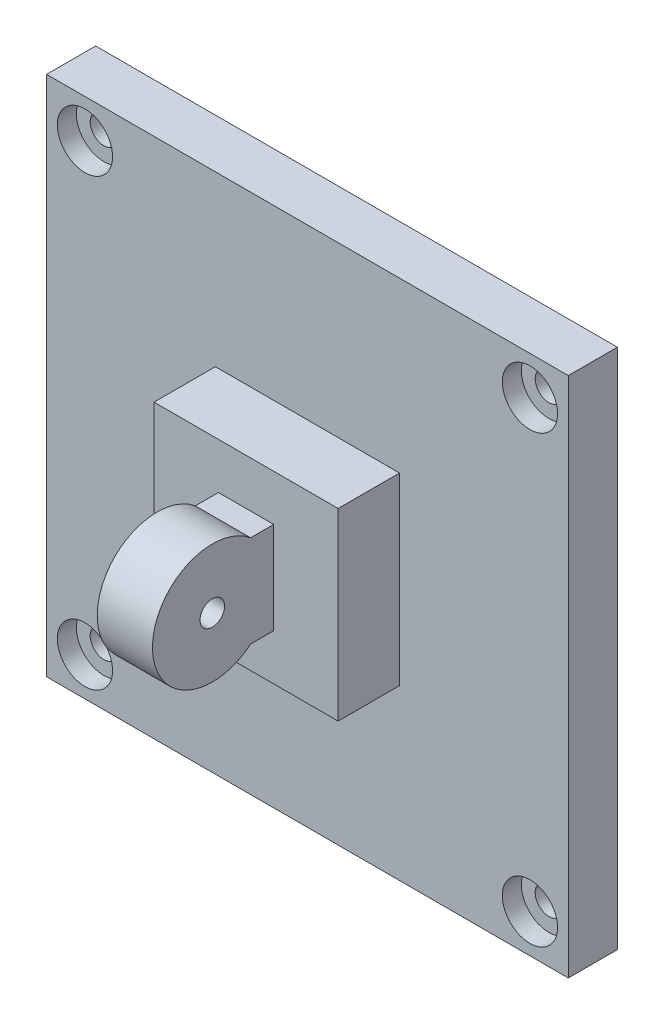
SolidWorks part; units mm, degrees
ref_plane "Front Plane" through (0, 0, 0) normal (0, 0, 1) x (1, 0, 0)
ref_plane "Top Plane" through (0, 0, 0) normal (0, 1, 0) x (1, 0, 0)
ref_plane "Right Plane" through (0, 0, 0) normal (1, 0, 0) x (0, 0, -1)
sketch "Esboço1" plane through (0, 0, 0) normal (0, 0, 1) x (1, 0, 0)
  line L0 (0, 36.75) -> (0, -36.75) construction
  line L9 (36.75, 0) -> (-36.75, 0) construction
  line L10 (-36.75, 36.75) -> (36.75, 36.75) construction
  line L11 (36.75, -36.75) -> (-36.75, -36.75) construction
  line L12 (-36.75, 36.75) -> (-36.75, -36.75) construction
  line L13 (36.75, 36.75) -> (36.75, -36.75) construction
  line L15 (-42.5, 42.5) -> (42.5, 42.5)
  line L16 (-42.5, 42.5) -> (-42.5, -42.5)
  line L17 (-42.5, -42.5) -> (42.5, -42.5)
  line L18 (42.5, 42.5) -> (42.5, -42.5)
  point P12 (0, 0)
  dimension "D1" = 85
  dimension "D2" = 85
  dimension "D3" = 73.5
  dimension "D4" = 73.5
extrude "Ressalto-extrusão1" add sketch "Esboço1" along normal blind 8
hole_wizard "Rebaixo para parafuso de máquina com cabeça panela de M41" positions "Esboço3" profile "Esboço4" counterbore size "M4" standard "Ansi Metric" end condition through all
sketch "Esboço3" plane through (0, 0, 8) normal (0, 0, 1) x (1, 0, 0)
  line L0 (-42.5, 42.5) -> (-42.5, -42.5) construction
  line L1 (-42.5, -42.5) -> (42.5, -42.5) construction
  line L2 (42.5, 42.5) -> (-42.5, 42.5) construction
  line L3 (0, 0) -> (0, 37.6222) construction
  point P0 (-36.25, 36.25)
  point P2 (-36.25, -36.25)
  point P16 (36.25, -36.25)
  point P17 (36.25, 36.25)
  dimension "D1" = 6.25
  dimension "D2" = 6.25
  dimension "D3" = 6.25
  dimension "D4" = 6.25
sketch "Esboço4" plane through (-36.25, 36.25, 8) normal (1, 0, 0) x (0, -1, 0)
  line L0 (0, 0) -> (0, 8)
  line L1 (0, 8) -> (2.25, 8)
  line L3 (2.25, 8) -> (2.25, 3.1)
  line L4 (2.25, 3.1) -> (4.5, 3.1)
  line L5 (4.5, 3.1) -> (4.5, 0)
  line L7 (4.5, 0) -> (0, 0)
  line L11 (0, -6.35) -> (0, 107.95) construction
  dimension "Thru Hole Dia." = 4.5
  dimension "Thru Hole Depth" = 8
  dimension "C'Bore Dia." = 9
  dimension "C'Bore Depth" = 3.1
sketch "Esboço5" plane through (0, 0, 8) normal (0, 0, 1) x (1, 0, 0)
  line L0 (-42.5, 0) -> (42.5, 0) construction
  line L1 (-15, 15) -> (15, 15)
  line L2 (-15, 15) -> (-15, -15)
  line L3 (-15, -15) -> (15, -15)
  line L4 (15, 15) -> (15, -15)
  line L5 (-42.5, 42.5) -> (-42.5, -42.5) construction
  line L6 (42.5, -42.5) -> (42.5, 42.5) construction
  line L7 (0, 42.5) -> (0, -42.5) construction
  line L8 (42.5, 42.5) -> (-42.5, 42.5) construction
  line L9 (-42.5, -42.5) -> (42.5, -42.5) construction
  line L10 (0, 15) -> (0, -15) construction
  line L11 (0, -15) -> (0, 0) construction
  dimension "D1" = 30
  dimension "D2" = 30
extrude "Ressalto-extrusão2" add sketch "Esboço5" along normal blind 20
sketch "Esboço6" plane through (15, 0, 0) normal (1, 0, 0) x (0, 0, -1)
  line L0 (-28, 0) -> (-8, 0) construction
  line L1 (-28, -15) -> (-28, 15) construction
  line L2 (-8, -42.5) -> (-8, 42.5) construction
  circle A0 centre (-28, 0) radius 10
extrude "Corte-extrusão1" cut sketch "Esboço6" against normal blind 10
sketch "Esboço7" plane through (-15, 0, 0) normal (-1, 0, 0) x (0, 0, 1)
  line L0 (8, 0) -> (28, 0) construction
  line L1 (8, 42.5) -> (8, -42.5) construction
  line L2 (28, 15) -> (28, -15) construction
  circle A0 centre (28, 0) radius 10
extrude "Corte-extrusão2" cut sketch "Esboço7" against normal blind 10
sketch "Esboço8" plane through (-15, 0, 0) normal (-1, 0, 0) x (0, 0, 1)
  line L1 (18, 10) -> (18, 15)
  line L2 (28, 15) -> (8, 15) construction
  line L3 (18, 15) -> (28, 15)
  line L4 (28, 15) -> (28, 10)
  line L6 (18, -10) -> (18, -15)
  line L7 (28, -15) -> (8, -15) construction
  line L8 (18, -15) -> (28, -15)
  line L9 (28, -15) -> (28, -10)
  line L10 (18, 10) -> (18, -10)
  line L11 (28, 10) -> (28, -10)
extrude "Corte-extrusão3" cut sketch "Esboço8" against normal through all
sketch "Esboço9" plane through (0, 0, 18) normal (0, 0, 1) x (1, 0, 0)
  line L0 (0, 15) -> (0, -15) construction
  line L2 (15, -15) -> (-15, -15) construction
  line L3 (0, 15) -> (0, 10) construction
  line L8 (0, 7.5) -> (0, -7.5) construction
  line L9 (-4.5, 7.5) -> (4.5, 7.5)
  line L10 (-4.5, 7.5) -> (-4.5, -7.5)
  line L11 (-4.5, -7.5) -> (4.5, -7.5)
  line L12 (4.5, 7.5) -> (4.5, -7.5)
  point P10 (0, 0)
  dimension "D1" = 9
  dimension "D2" = 15
extrude "Ressalto-extrusão3" add sketch "Esboço9" along normal blind 10
sketch "Esboço10" plane through (-4.5, 0, 0) normal (-1, 0, 0) x (0, 0, 1)
  line L0 (18, 0) -> (28, 0) construction
  line L1 (18, 15) -> (18, -15) construction
  line L2 (28, 7.5) -> (28, -7.5) construction
  circle A0 centre (28, 0) radius 9.75
  dimension "D1" = 19.5
extrude "Ressalto-extrusão4" add sketch "Esboço10" against normal blind 9
sketch "Esboço11" plane through (-4.5, 0, 0) normal (-1, 0, 0) x (0, 0, 1)
  circle A2 centre (28, 0) radius 2
  circle A3 centre (28, 0) radius 2
  dimension "D1" = 0
extrude "Corte-extrusão4" cut sketch "Esboço11" against normal through all
